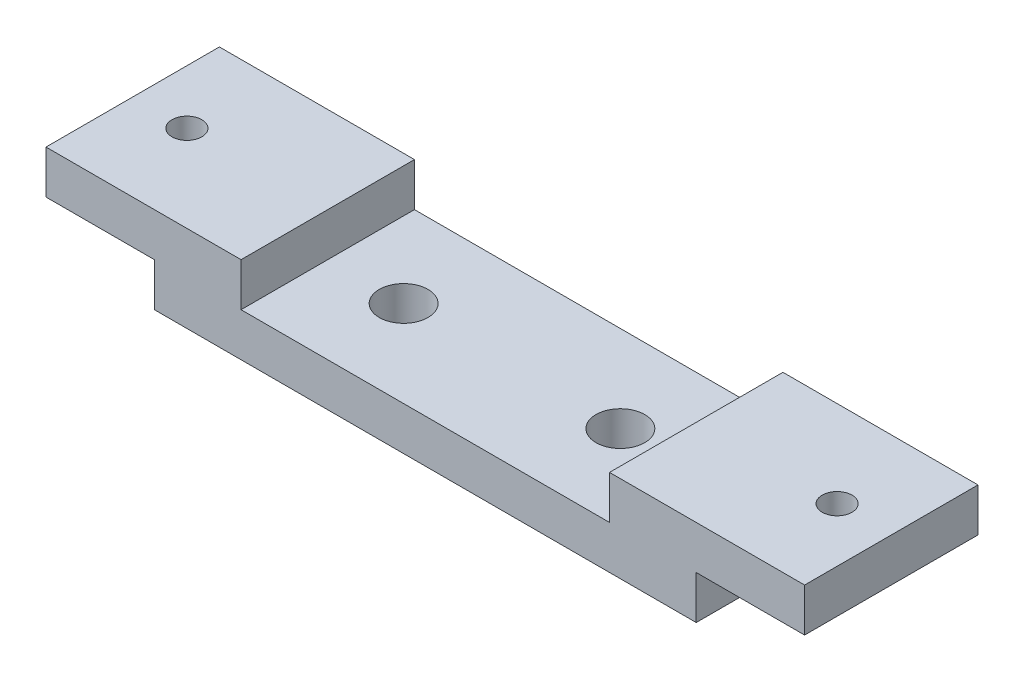
SolidWorks part; units mm, degrees
ref_plane "Ebene vorne" through (0, 0, 0) normal (0, 0, 1) x (1, 0, 0)
ref_plane "Ebene oben" through (0, 0, 0) normal (0, 1, 0) x (1, 0, 0)
ref_plane "Ebene rechts" through (0, 0, 0) normal (1, 0, 0) x (0, 0, -1)
sketch "Skizze1" plane through (0, 0, 0) normal (0, 0, 1) x (1, 0, 0)
  line L0 (-70, 16) -> (-34, 16)
  line L1 (-34, 8) -> (34, 8)
  line L2 (34, 8) -> (34, 16)
  line L3 (34, 16) -> (70, 16)
  line L4 (70, 16) -> (70, 8)
  line L5 (70, 8) -> (50, 8)
  line L7 (-50, 8) -> (-70, 8)
  line L8 (-70, 8) -> (-70, 16)
  line L9 (-34, 16) -> (-34, 8)
  line L10 (-50, 8) -> (-50, 0)
  line L11 (-50, 0) -> (50, 0)
  line L12 (50, 0) -> (50, 8)
  point P12 (0, 0)
  point P13 (34, 12)
  point P15 (0, 8)
  dimension "D1" = 8
  dimension "D2" = 68
  dimension "D3" = 68
  dimension "D4" = 8
  dimension "D5" = 8
  dimension "D6" = 16
  dimension "D7" = 20
extrude "Aufsatz-Linear austragen1" add sketch "Skizze1" along normal blind 32
hole_wizard "Ø9.0 (9) Durchmesser Bohrung1" positions "3D-Skizze4" profile "Skizze5" hole size "Ø9.0" standard "ANSI Metrisch" end condition through all
sketch3d "3D-Skizze4"
  line L5 (-34, 8, 16) -> (34, 8, 16) construction
  line L6 (-34, 8, 32) -> (-34, 8, 0) construction
  line L7 (34, 8, 32) -> (34, 8, 0) construction
  point P0 (20, 8, 16)
  point P2 (-20, 8, 16)
  point P47 (-20, 8, 16)
  point P49 (20, 8, 16)
  dimension "D1" = 40
  dimension "D2" = 14
sketch "Skizze5" plane through (20, 8, 16) normal (1, 0, 0) x (0, 0, 1)
  line L0 (0, 0) -> (0, 8)
  line L1 (0, 8) -> (4.5, 8)
  line L2 (4.5, 8) -> (4.5, 0)
  line L5 (4.5, 0) -> (0, 0)
  line L11 (0, -6.35) -> (0, 107.95) construction
  dimension "Bohrerdurchmesser" = 9
  dimension "Bohrungstiefe" = 8
hole_wizard "Ø5.5 (5.5) Durchmesser Bohrung1" positions "3D-Skizze5" profile "Skizze6" hole size "Ø5.5" standard "ANSI Metrisch" end condition through all
sketch3d "3D-Skizze5"
  line L0 (50, 8, 0) -> (70, 8, 32) construction
  line L2 (70, 8, 0) -> (50, 8, 32) construction
  line L4 (-70, 8, 0) -> (-50, 8, 32) construction
  line L6 (-50, 8, 0) -> (-70, 8, 32) construction
  point P0 (-60, 8, 16)
  point P2 (60, 8, 16)
sketch "Skizze6" plane through (-60, 8, 16) normal (1, 0, 0) x (0, 0, -1)
  line L0 (0, 0) -> (0, 8)
  line L1 (0, 8) -> (2.75, 8)
  line L2 (2.75, 8) -> (2.75, 0)
  line L5 (2.75, 0) -> (0, 0)
  line L11 (0, -6.35) -> (0, 107.95) construction
  dimension "Bohrerdurchmesser" = 5.5
  dimension "Bohrungstiefe" = 8
